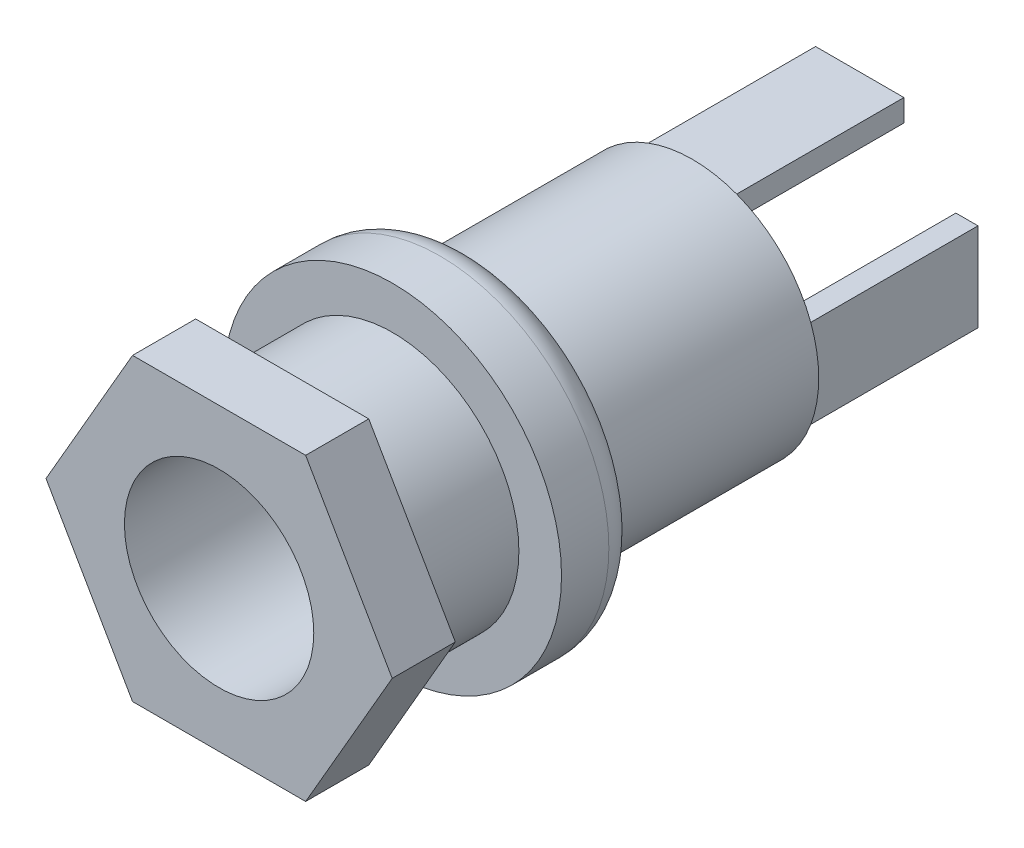
SolidWorks part; units mm, degrees
ref_plane "Alzado" through (0, 0, 0) normal (0, 0, 1) x (1, 0, 0)
ref_plane "Planta" through (0, 0, 0) normal (0, 1, 0) x (1, 0, 0)
ref_plane "Vista lateral" through (0, 0, 0) normal (1, 0, 0) x (0, 0, -1)
sketch "Croquis1" plane through (0, 0, 0) normal (0, 0, 1) x (1, 0, 0)
  circle A0 centre (0, 0) radius 4
  circle A1 centre (0, 0) radius 3
  dimension "D1" = 8
  dimension "D2" = 1
extrude "Saliente-Extruir1" add sketch "Croquis1" against normal blind 5.5
sketch "Croquis2" plane through (0, 0, -5.5) normal (0, 0, -1) x (-1, 0, 0)
  circle A0 centre (0, 0) radius 3 construction
  circle A1 centre (0, 0) radius 3
  circle A2 centre (0, 0) radius 5.35
  dimension "D1" = 10.7
extrude "Saliente-Extruir2" add sketch "Croquis2" along normal blind 2.5
fillet "Redondeo1" radius 1 1 edges at (-5.35, 0, -8)
sketch "Croquis3" plane through (0, 0, -8) normal (0, 0, -1) x (-1, 0, 0)
  circle A0 centre (0, 0) radius 4
  dimension "D1" = 8
extrude "Saliente-Extruir3" add sketch "Croquis3" along normal blind 7
sketch "Croquis4" plane through (0, 0, -15) normal (0, 0, -1) x (-1, 0, 0)
  line L0 (0, 0) -> (0, 4) construction
  line L1 (0, 0) -> (-4, 0) construction
  line L2 (0, 0) -> (4, 0) construction
  line L4 (1.4, 3.047) -> (-1.4, 3.047)
  line L5 (1.4, 3.047) -> (1.4, 3.747)
  line L6 (1.4, 3.747) -> (-1.4, 3.747)
  line L7 (-1.4, 3.047) -> (-1.4, 3.747)
  line L8 (1.4, 3.047) -> (-1.4, 3.747) construction
  line L9 (1.4, 3.747) -> (-1.4, 3.047) construction
  line L10 (-3.047, -1.4) -> (-3.747, -1.4)
  line L11 (-3.047, -1.4) -> (-3.047, 1.4)
  line L12 (-3.047, 1.4) -> (-3.747, 1.4)
  line L13 (-3.747, -1.4) -> (-3.747, 1.4)
  line L14 (-3.047, -1.4) -> (-3.747, 1.4) construction
  line L15 (-3.047, 1.4) -> (-3.747, -1.4) construction
  line L16 (3.047, -1.4) -> (3.747, -1.4)
  line L17 (3.047, -1.4) -> (3.047, 1.4)
  line L18 (3.047, 1.4) -> (3.747, 1.4)
  line L19 (3.747, -1.4) -> (3.747, 1.4)
  line L20 (3.047, -1.4) -> (3.747, 1.4) construction
  line L21 (3.047, 1.4) -> (3.747, -1.4) construction
  circle A0 centre (0, 0) radius 4 construction
  point P5 (0, 3.397)
  point P13 (-3.397, 0)
  point P18 (3.397, 0)
  dimension "D1" = 0.7
  dimension "D2" = 2.8
extrude "Saliente-Extruir4" add sketch "Croquis4" along normal blind 5.3
sketch "Croquis5" plane through (0, 0, 0) normal (0, 0, 1) x (1, 0, 0)
  line L1 (5.4848, 0) -> (2.7424, 4.75)
  line L2 (2.7424, 4.75) -> (-2.7424, 4.75)
  line L3 (-2.7424, 4.75) -> (-5.4848, 0)
  line L4 (-5.4848, 0) -> (-2.7424, -4.75)
  line L5 (-2.7424, -4.75) -> (2.7424, -4.75)
  line L6 (2.7424, -4.75) -> (5.4848, 0)
  circle A0 centre (0, 0) radius 4.75 construction
  circle A1 centre (0, 0) radius 4 construction
  circle A2 centre (0, 0) radius 4
  dimension "D1" = 9.5
extrude "Saliente-Extruir5" add sketch "Croquis5" against normal blind 2
